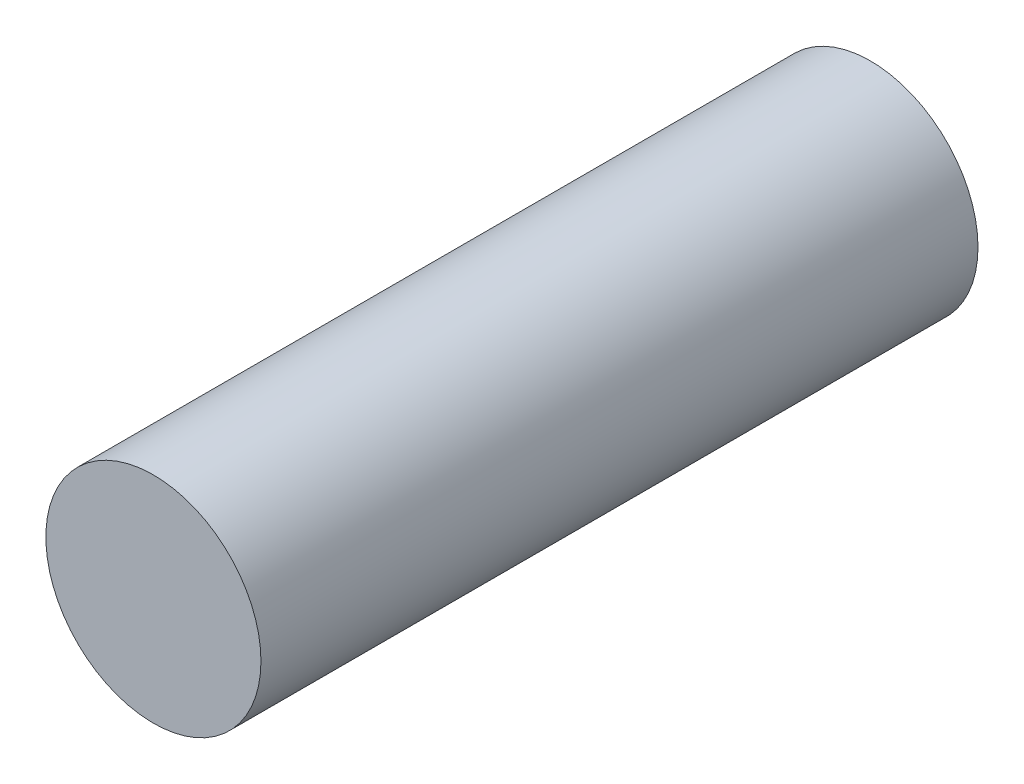
SolidWorks part; units mm, degrees
ref_plane "Front Plane" through (0, 0, 0) normal (0, 0, 1) x (1, 0, 0)
ref_plane "Top Plane" through (0, 0, 0) normal (0, 1, 0) x (1, 0, 0)
ref_plane "Right Plane" through (0, 0, 0) normal (1, 0, 0) x (0, 0, -1)
sketch "Sketch1" plane through (0, 0, 0) normal (0, 0, 1) x (1, 0, 0)
  circle A0 centre (0, 0) radius 6
  dimension "D1" = 12
extrude "Extrude1" add sketch "Sketch1" along normal mid plane 40
